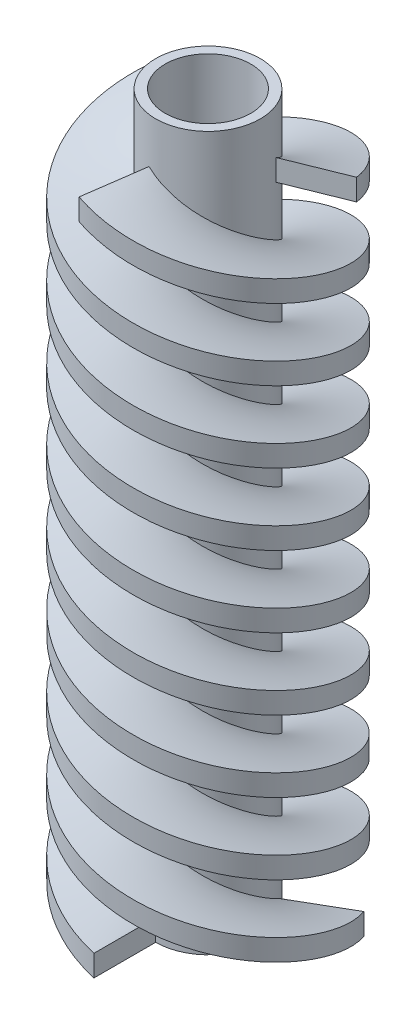
SolidWorks part; units mm, degrees
ref_plane "Ebene vorne" through (0, 0, 0) normal (0, 0, 1) x (1, 0, 0)
ref_plane "Ebene oben" through (0, 0, 0) normal (0, 1, 0) x (1, 0, 0)
ref_plane "Ebene rechts" through (0, 0, 0) normal (1, 0, 0) x (0, 0, -1)
sketch "Skizze1" plane through (0, 0, 0) normal (0, 1, 0) x (1, 0, 0)
  circle A0 centre (0, 0) radius 11
  circle A1 centre (0, 0) radius 9
  dimension "D1" = 22
  dimension "D2" = 18
extrude "Aufsatz-Linear austragen1" add sketch "Skizze1" along normal blind 150
sketch "Skizze2" plane through (0, 0, 0) normal (0, 1, 0) x (1, 0, 0)
  circle A0 centre (0, 0) radius 11 construction
  circle A1 centre (0, 0) radius 11
curve "Spirale/Helix1" pitch 45 height 136 turns 3.0222
sketch "Skizze3" plane through (0, 0, 0) normal (1, 0, 0) x (0, 0, -1)
  line L0 (0, -4.6528) -> (0, 154.2684) construction
  line L1 (-24, 4.5) -> (-11, 4.5)
  line L2 (-24, 4.5) -> (-24, 0)
  line L3 (-24, 0) -> (-11, 0)
  line L4 (-11, 4.5) -> (-11, 0)
  line L5 (-11, 150) -> (-11, 0) construction
  spline S0 degree 3 poles (-11, 0) (-11, 0.9401) (-10.4186, 2.8353) (-7.9371, 5.6661) (-4.2296, 8.5001) (0.1314, 11.3333) (4.472, 14.1667) (8.1218, 17) (10.517, 19.8333) (11.2876, 22.6667) (10.3146, 25.5) (7.7481, 28.3333) (3.9848, 31.1667) (-0.394, 34) (-4.712, 36.8333) (-8.3021, 39.6667) (-10.6098, 42.5) (-11.2785, 45.3333) (-10.2049, 48.1667) (-7.5549, 51) (-3.7379, 53.8333) (0.6565, 56.6667) (4.9495, 59.5) (8.478, 62.3333) (10.6968, 65.1667) (11.2632, 68) (10.0897, 70.8333) (7.3577, 73.6667) (3.489, 76.5) (-0.9186, 79.3333) (-5.1843, 82.1667) (-8.6492, 85) (-10.778, 87.8333) (-11.2418, 90.6667) (-9.9691, 93.5) (-7.1564, 96.3333) (-3.2382, 99.1667) (1.1802, 102) (5.4163, 104.8333) (8.8157, 107.6667) (10.8533, 110.5) (11.2143, 113.3333) (9.843, 116.1667) (6.9512, 119) (2.9856, 121.8333) (-1.4412, 124.6667) (-5.6454, 127.4999) (-8.9773, 130.3339) (-10.9232, 133.1647) (-11.0939, 135.0599) (-10.8929, 136) knots 0 0 0 0 0.020833 0.041667 0.0625 0.083333 0.104167 0.125 0.145833 0.166667 0.1875 0.208333 0.229167 0.25 0.270833 0.291667 0.3125 0.333333 0.354167 0.375 0.395833 0.416667 0.4375 0.458333 0.479167 0.5 0.520833 0.541667 0.5625 0.583333 0.604167 0.625 0.645833 0.666667 0.6875 0.708333 0.729167 0.75 0.770833 0.791667 0.8125 0.833333 0.854167 0.875 0.895833 0.916667 0.9375 0.958333 0.979167 1 1 1 1 construction
  dimension "D1" = 4.5
  dimension "D2" = 48
sweep "Austragung1" add profiles "Skizze3" path "Spirale/Helix1"
pattern_circular "Kreismuster1" count 3 over 360 about axis through (0, 150, 0) along (0, -1, 0) of "Austragung1"
